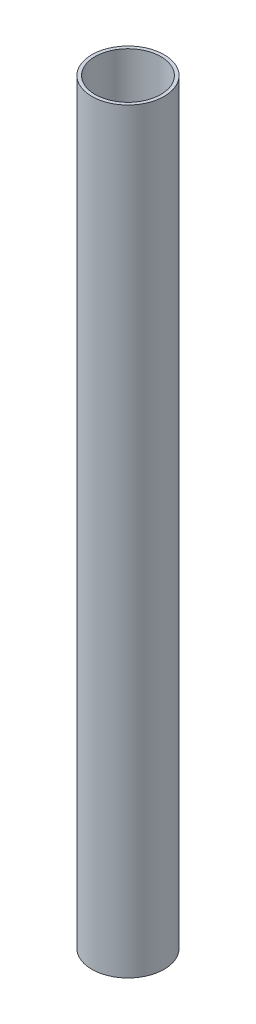
SolidWorks part; units mm, degrees
ref_plane "前视基准面" through (0, 0, 0) normal (0, 0, 1) x (1, 0, 0)
ref_plane "上视基准面" through (0, 0, 0) normal (0, 1, 0) x (1, 0, 0)
ref_plane "右视基准面" through (0, 0, 0) normal (1, 0, 0) x (0, 0, -1)
sketch "草图1" plane through (0, 0, 0) normal (0, 1, 0) x (1, 0, 0)
  circle A0 centre (0, 0) radius 11
  circle A1 centre (0, 0) radius 10
  dimension "D1" = 22
  dimension "D2" = 20
extrude "凸台-拉伸1" add sketch "草图1" along normal blind 230
